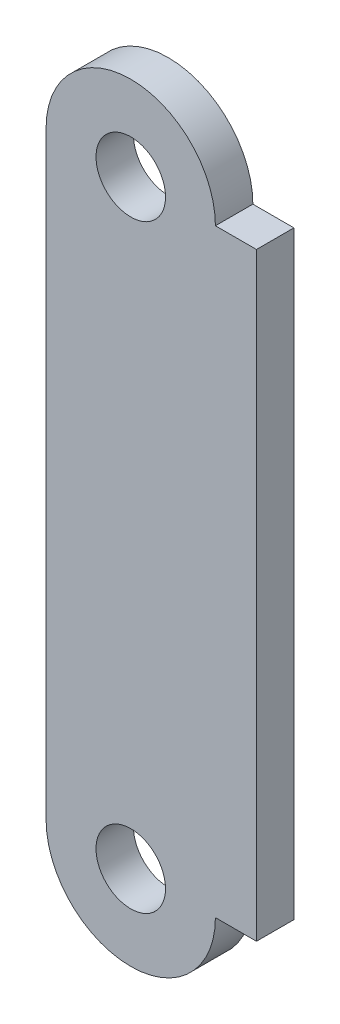
SolidWorks part; units mm, degrees
ref_plane "Front Plane" through (0, 0, 0) normal (0, 0, 1) x (1, 0, 0)
ref_plane "Top Plane" through (0, 0, 0) normal (0, 1, 0) x (1, 0, 0)
ref_plane "Right Plane" through (0, 0, 0) normal (1, 0, 0) x (0, 0, -1)
sketch "Sketch1" plane through (0, 0, 0) normal (0, 0, 1) x (1, 0, 0)
  line L0 (0, 12.7) -> (0, -12.7) construction
  line L1 (3.589, 12.7) -> (3.589, -12.7)
  line L2 (-3.589, 12.7) -> (-3.589, -12.7)
  arc A0 (3.589, 12.7) -> (-3.589, 12.7) centre (0, 12.7) ccw
  arc A1 (-3.589, -12.7) -> (3.589, -12.7) centre (0, -12.7) ccw
  point P3 (0, 0)
  dimension "D2" = 3.589
  dimension "D1" = 25.4
extrude "Boss-Extrude1" add sketch "Sketch1" along normal blind 1.5875
hole_wizard "#4 Clearance Hole1" positions "Sketch3" profile "Sketch2" hole size "#4" standard "ANSI Inch"
sketch "Sketch3" plane through (0, 0, 1.5875) normal (0, 0, 1) x (1, 0, 0)
  point P0 (0, 12.7)
  point P3 (0, -12.7)
sketch "Sketch2" plane through (0, 12.7, 1.5875) normal (1, 0, 0) x (0, -1, 0)
  line L0 (0, 0) -> (0, 4.1872)
  line L1 (0, 4.1872) -> (1.4732, 3.302)
  line L2 (1.4732, 3.302) -> (1.4732, 0)
  line L5 (1.4732, 0) -> (0, 0)
  line L10 (0, 4.1872) -> (-1.4732, 3.302) construction
  line L11 (0, -6.35) -> (0, 107.95) construction
  dimension "Hole Dia." = 2.9464
  dimension "Hole Depth" = 3.302
  dimension "Drill Angle" = 118
sketch "Sketch5" plane through (0, 0, 1.5875) normal (0, 0, 1) x (1, 0, 0)
  line L1 (3.589, 12.7) -> (5.3289, 12.7)
  line L2 (3.589, 12.7) -> (3.589, -12.7)
  line L3 (3.589, -12.7) -> (5.3289, -12.7)
  line L4 (5.3289, 12.7) -> (5.3289, -12.7)
  dimension "D1" = 1.7399
extrude "Boss-Extrude2" add sketch "Sketch5" against normal up to surface (1.5875 mm away) up to face at (1.4732, 12.7, 0)
